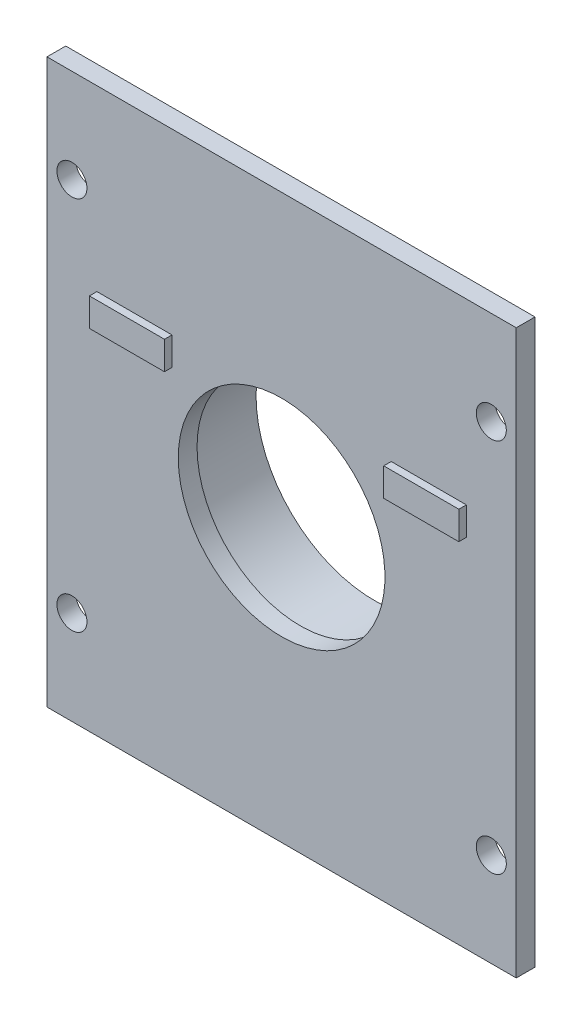
SolidWorks part; units mm, degrees
ref_plane "Front" through (0, 0, 0) normal (0, 0, 1) x (1, 0, 0)
ref_plane "Top" through (0, 0, 0) normal (0, 1, 0) x (1, 0, 0)
ref_plane "Right" through (0, 0, 0) normal (1, 0, 0) x (0, 0, -1)
sketch "Sketch3" plane through (0, 0, 0) normal (0, 0, 1) x (1, 0, 0)
  line L0 (31.75, 0) -> (31.75, 76.2) construction
  line L1 (0, 0) -> (63.5, 0)
  line L2 (0, 0) -> (0, 76.2)
  line L3 (0, 76.2) -> (63.5, 76.2)
  line L4 (63.5, 0) -> (63.5, 76.2)
  line L5 (0, 38.1) -> (63.5, 38.1) construction
extrude "Boss-Extrude2" add sketch "Sketch3" along normal blind 2.54
ref_plane "Plane2" through (0, 0, 0) normal (0, 0, -1) x (-1, 0, 0)
sketch "Sketch4" plane through (0, 0, 0) normal (0, 0, -1) x (-1, 0, 0)
  line L0 (-31.75, 76.2) -> (-31.75, 0) construction
  line L1 (-63.5, 76.2) -> (0, 76.2) construction
  line L2 (0, 0) -> (-63.5, 0) construction
  line L3 (0, 38.1) -> (-63.5, 38.1) construction
  line L4 (0, 76.2) -> (0, 0) construction
  line L5 (-63.5, 0) -> (-63.5, 76.2) construction
  circle A0 centre (-31.75, 38.1) radius 16
  circle A1 centre (-31.75, 38.1) radius 17.27
extrude "Boss-Extrude3" add sketch "Sketch4" along normal blind 10
sketch "Sketch5" plane through (0, 0, 0) normal (0, 0, -1) x (-1, 0, 0)
  circle A0 centre (-31.75, 38.1) radius 13.984
extrude "Cut-Extrude1" cut sketch "Sketch5" against normal blind 10.0076
ref_plane "Plane3" through (0, 0, 0) normal (0, -1, 0) x (-1, 0, 0)
sketch "Sketch8" plane through (0, 0, 0) normal (0, 0, -1) x (-1, 0, 0)
  line L0 (-63.5, 38.1) -> (0, 38.1) construction
  line L1 (-63.5, 0) -> (-63.5, 76.2) construction
  line L2 (-3.375, 76.2) -> (-3.375, 63.5) construction
  line L3 (-1.397, 0) -> (1.397, 0) construction
  line L4 (-31.75, 76.2) -> (-31.75, 0) construction
  line L5 (-63.5, 76.2) -> (0, 76.2) construction
  line L6 (-3.375, 12.7) -> (0, 12.7) construction
  line L7 (0, 76.2) -> (0, 0) construction
  line L8 (-3.375, 12.7) -> (-3.375, 0) construction
  line L9 (-3.375, 63.5) -> (0, 63.5) construction
  circle A0 centre (-3.375, 63.5) radius 2.032
  circle A1 centre (-60.125, 63.5) radius 2.032
  circle A2 centre (-60.125, 12.7) radius 2.032
  circle A3 centre (-3.375, 12.7) radius 2.032
extrude "Cut-Extrude2" cut sketch "Sketch8" against normal through all
sketch "Sketch9" plane through (0, 0, 2.54) normal (0, 0, 1) x (1, 0, 0)
  line L1 (46.5836, 48.26) -> (56.7436, 48.26)
  line L2 (56.7436, 52.07) -> (56.7436, 48.26)
  line L3 (46.5836, 52.07) -> (56.7436, 52.07)
  line L4 (6.7564, 52.07) -> (6.7564, 48.26)
  line L7 (16.9164, 48.26) -> (16.9164, 52.07)
  line L8 (46.5836, 48.26) -> (46.5836, 52.07)
  line L9 (6.7564, 48.26) -> (16.9164, 48.26)
  line L10 (16.9164, 52.07) -> (6.7564, 52.07)
  line L11 (63.5, 0) -> (63.5, 76.2) construction
  line L12 (0, 76.2) -> (0, 0) construction
  dimension "D1" = 16.9164
  dimension "D2" = 16.9164
extrude "Boss-Extrude4" add sketch "Sketch9" along normal blind 1.016
